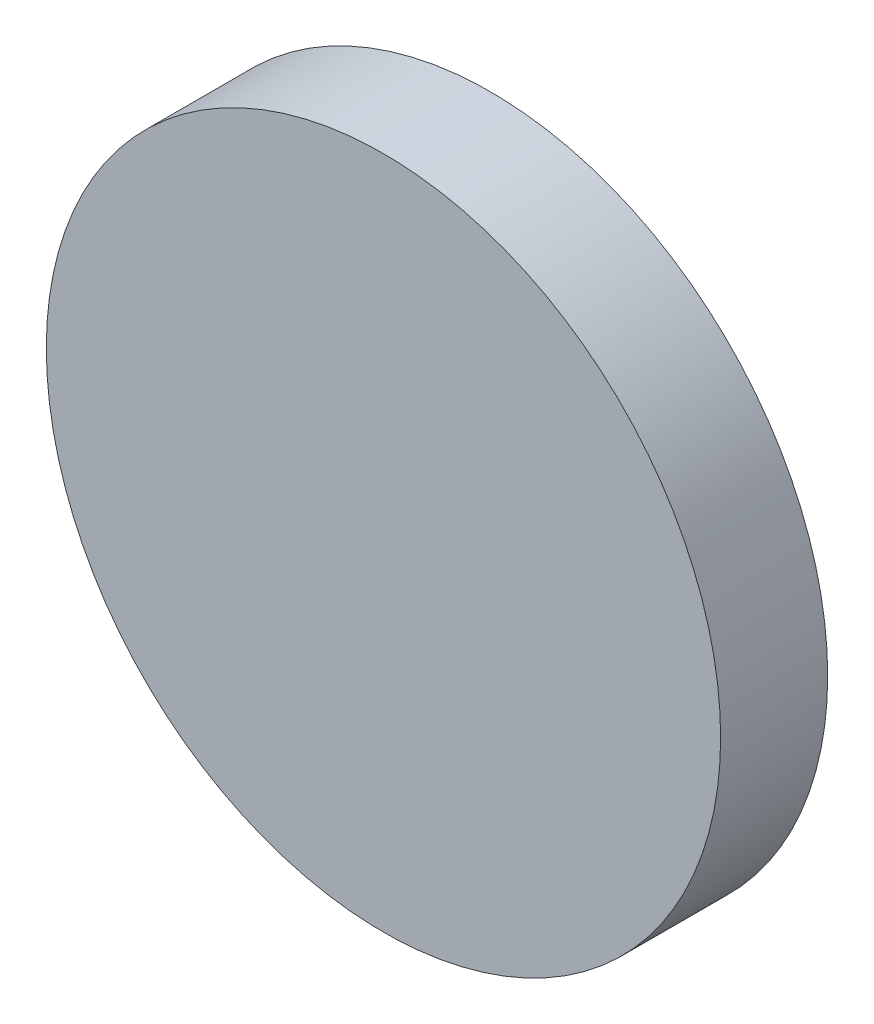
SolidWorks part; units mm, degrees
ref_plane "Front Plane" through (0, 0, 0) normal (0, 0, 1) x (1, 0, 0)
ref_plane "Top Plane" through (0, 0, 0) normal (0, 1, 0) x (1, 0, 0)
ref_plane "Right Plane" through (0, 0, 0) normal (1, 0, 0) x (0, 0, -1)
sketch "Sketch1" plane through (0, 0, 0) normal (0, 0, 1) x (1, 0, 0)
  circle A0 centre (0, 0) radius 4 construction
  circle A1 centre (0, 0) radius 5
  dimension "D1" = 8
  dimension "D2" = 1
extrude "Boss-Extrude1" add sketch "Sketch1" along normal blind 1.5875
